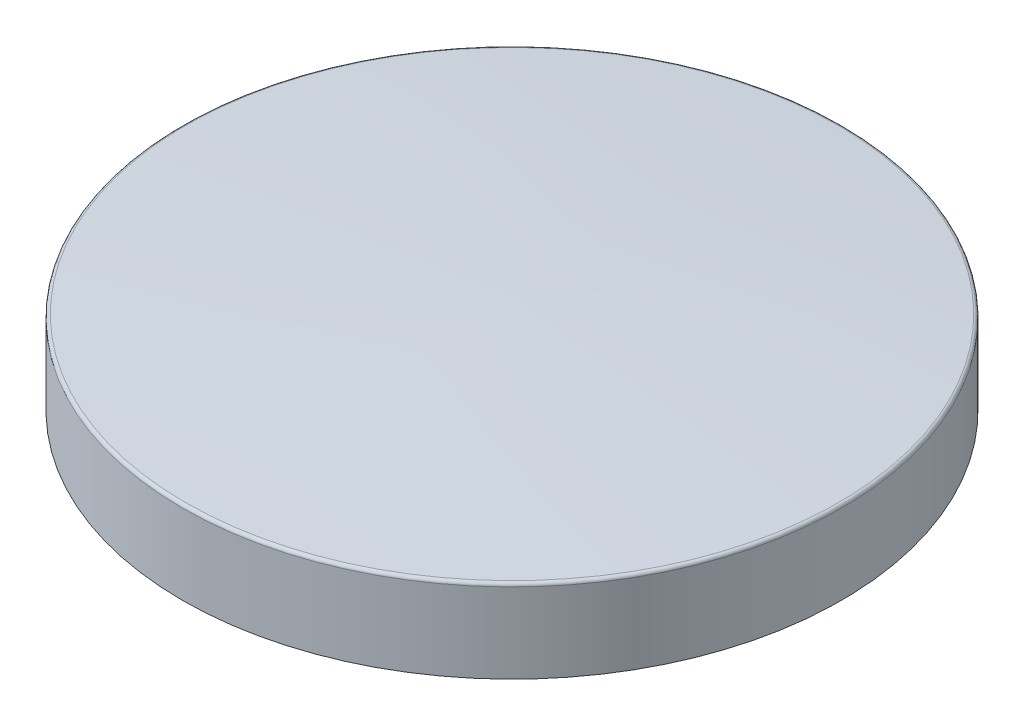
SolidWorks part; units mm, degrees
ref_plane "Front Plane" through (0, 0, 0) normal (0, 0, 1) x (1, 0, 0)
ref_plane "Top Plane" through (0, 0, 0) normal (0, 1, 0) x (1, 0, 0)
ref_plane "Right Plane" through (0, 0, 0) normal (1, 0, 0) x (0, 0, -1)
sketch "Sketch2" plane through (0, 0, 0) normal (0, 0, 1) x (1, 0, 0)
  line L0 (0, 0) -> (0, -29.7561) construction
  line L1 (0, 0) -> (0, -2.9941)
  line L2 (0, -2.9941) -> (10, -2.9941)
  line L3 (10, -2.9941) -> (10, -0.4764)
  arc A0 (0, 0) -> (10, -0.4764) centre (-4.2889, -195.2289) cw
  dimension "D1" = 10
  dimension "D2" = 195.276
revolve "Revolve1" add sketch "Sketch2" angle 360 about L1
fillet "Fillet1" radius 0.1 1 edges at (0, -0.4764, 10)
sketch3d "3DSketch1"
  line L0 (-4.3768, 0, 0) -> (-4.3768, 0, -1.2467) construction
  line L1 (-4.3768, 0, -1.2467) -> (-3.6713, 0, -1.2467) construction
  line L2 (-3.6713, 0, -1.2467) -> (-3.6713, 0, -0.3265) construction
  line L3 (-3.6713, 0, -0.3265) -> (-0.3893, 0, -0.3265) construction
  line L4 (-0.3893, 0, -0.3265) -> (-0.3893, 0, -1.2467)
  line L5 (-0.3893, 0, -1.2467) -> (0.3162, 0, -1.2467)
  line L6 (0.3162, 0, -1.2467) -> (0.3162, 0, -0.3265)
  line L7 (0.3162, 0, -0.3265) -> (3.997, 0, -0.3265)
  line L8 (3.997, 0, -0.3265) -> (3.997, 0, -1.2467)
  line L9 (3.997, 0, -1.2467) -> (4.7332, 0, -1.2467)
  line L10 (4.7332, 0, -1.2467) -> (4.7332, 0, 1.2467)
  line L11 (-3.6713, 0, -1.2467) -> (-3.6713, 0, -0.3265)
  line L12 (-3.6713, 0, -0.3265) -> (-0.3893, 0, -0.3265)
  line L13 (-3.6713, 0, -1.2467) -> (-4.3768, 0, -1.2467)
  line L14 (-4.3768, 0, -1.2467) -> (-4.3768, 0, 1.2467)
  line L15 (-4.7675, 0, 0) -> (5.2719, 0, 0) construction
  line L16 (3.997, 0, 1.2467) -> (4.7332, 0, 1.2467)
  line L17 (3.997, 0, 0.3265) -> (3.997, 0, 1.2467)
  line L18 (0.3162, 0, 0.3265) -> (3.997, 0, 0.3265)
  line L19 (0.3162, 0, 1.2467) -> (0.3162, 0, 0.3265)
  line L20 (-0.3893, 0, 1.2467) -> (0.3162, 0, 1.2467)
  line L21 (-0.3893, 0, 0.3265) -> (-0.3893, 0, 1.2467)
  line L22 (-3.6713, 0, 0.3265) -> (-0.3893, 0, 0.3265)
  line L23 (-3.6713, 0, 1.2467) -> (-3.6713, 0, 0.3265)
  line L24 (-3.6713, 0, 1.2467) -> (-4.3768, 0, 1.2467)
  point P15 (4.7332, 0, 0)
sketch "Sketch14" plane through (0, -2.9941, 0) normal (0, -1, 0) x (-1, 0, 0)
  text T0 "1 3 5\r\n2 4 R" font "Century Gothic" height 4
extrude "Cut-Extrude30" cut sketch "Sketch14" against normal blind 2.5
sketch "Sketch15" plane through (0, -2.9941, 0) normal (0, -1, 0) x (-1, 0, 0)
  line L0 (0, 0) -> (7.6005, 0)
  line L1 (4.8488, 1.0197) -> (4.0488, 1.0197)
  line L2 (4.0488, 1.0197) -> (4.0488, 0.2934)
  line L3 (4.0488, 0.2934) -> (0.3488, 0.2934)
  line L4 (0.3488, 0.2934) -> (0.3488, 1.0197)
  line L5 (0.3488, 1.0197) -> (-0.4512, 1.0197)
  line L6 (-0.4512, 1.0197) -> (-0.4512, 0.2934)
  line L7 (-0.4512, 0.2934) -> (-4.1512, 0.2934)
  line L8 (-4.1512, 0.2934) -> (-4.1512, 1.0197)
  line L9 (-4.1512, 1.0197) -> (-4.9512, 1.0197)
  line L10 (-4.9512, 1.0197) -> (-4.9512, -1.0197)
  line L11 (4.8488, 1.0197) -> (4.8488, -1.0197)
  line L12 (-4.1512, -1.0197) -> (-4.9512, -1.0197)
  line L13 (-4.1512, -0.2934) -> (-4.1512, -1.0197)
  line L14 (-0.4512, -0.2934) -> (-4.1512, -0.2934)
  line L15 (-0.4512, -1.0197) -> (-0.4512, -0.2934)
  line L16 (0.3488, -1.0197) -> (-0.4512, -1.0197)
  line L17 (0.3488, -0.2934) -> (0.3488, -1.0197)
  line L18 (4.0488, -0.2934) -> (0.3488, -0.2934)
  line L19 (4.0488, -1.0197) -> (4.0488, -0.2934)
  line L20 (4.8488, -1.0197) -> (4.0488, -1.0197)
  point P6 (-4.9512, 0)
  point P25 (4.8488, 0)
  dimension "D1" = 0.8
  dimension "D2" = 0.8
  dimension "D3" = 0.8
  dimension "D4" = 3.7
  dimension "D5" = 3.7
  dimension "D6" = 1.0197
  dimension "D8" = 0.7263
extrude "Cut-Extrude32" cut sketch "Sketch15" against normal blind 2.5 contours L3 L4 L5 L6 L7 L8 L9 L10 L12 L13 L14 L15 L16 L17 L18 L19 L20 L11 L1 L2
